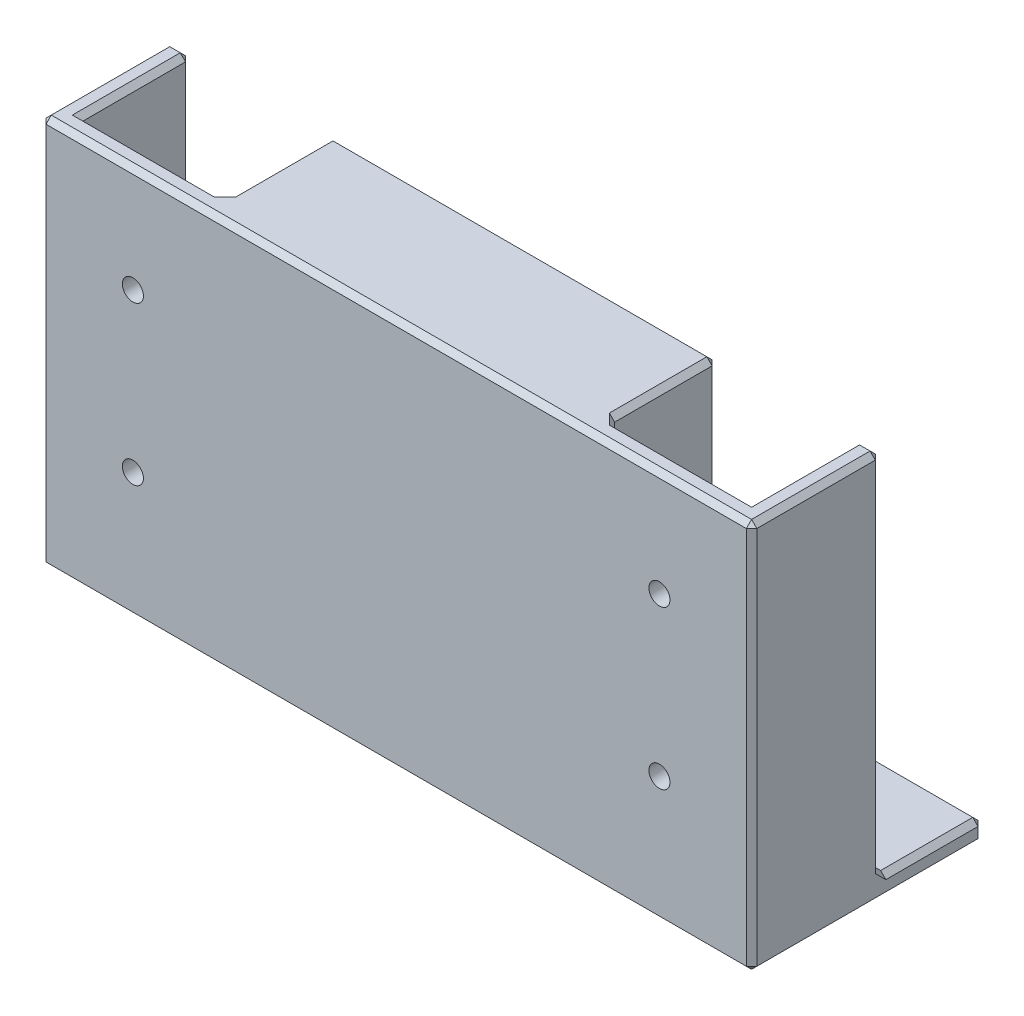
SolidWorks part; units mm, degrees
ref_plane "Front" through (0, 0, 0) normal (0, 0, 1) x (1, 0, 0)
ref_plane "Top" through (0, 0, 0) normal (0, 1, 0) x (1, 0, 0)
ref_plane "Right" through (0, 0, 0) normal (1, 0, 0) x (0, 0, -1)
sketch "Sketch1" plane through (0, 0, 0) normal (0, 1, 0) x (1, 0, 0)
  line L0 (-80.645, 15.56) -> (-85.725, 15.56)
  line L1 (85.725, 15.56) -> (80.645, 15.56)
  line L2 (85.725, 15.56) -> (85.725, -15.56)
  line L3 (85.725, -15.56) -> (-85.725, -15.56)
  line L4 (-85.725, 15.56) -> (-85.725, -15.56)
  line L5 (85.725, 15.56) -> (-85.725, -15.56) construction
  line L6 (85.725, -15.56) -> (-85.725, 15.56) construction
  line L7 (46.355, 15.56) -> (-46.355, 15.56)
  line L8 (-80.645, 15.56) -> (-80.645, -10.48)
  line L9 (-80.645, -10.48) -> (-46.355, -10.48)
  line L10 (-46.355, 15.56) -> (-46.355, -10.48)
  line L11 (-80.645, 15.56) -> (-46.355, -10.48) construction
  line L12 (-80.645, -10.48) -> (-46.355, 15.56) construction
  line L14 (80.645, 15.56) -> (80.645, -10.48)
  line L15 (80.645, -10.48) -> (46.355, -10.48)
  line L16 (46.355, 15.56) -> (46.355, -10.48)
  line L17 (80.645, 15.56) -> (46.355, -10.48) construction
  line L18 (80.645, -10.48) -> (46.355, 15.56) construction
  point P0 (0, 0)
  point P9 (-63.5, 2.54)
  point P14 (63.5, 2.54)
extrude "Boss-Extrude2" add sketch "Sketch1" along normal mid plane 88.9
shell "Shell3" thickness 5.08
sketch "Sketch7" plane through (0, -44.45, 0) normal (0, -1, 0) x (1, 0, 0)
  line L0 (80.645, 10.48) -> (46.355, 10.48) construction
  line L1 (85.725, 15.56) -> (-85.725, 15.56)
  line L2 (85.725, 15.56) -> (85.725, -40.32)
  line L3 (85.725, -40.32) -> (-85.725, -40.32)
  line L4 (-85.725, 15.56) -> (-85.725, -40.32)
  line L5 (85.725, 15.56) -> (-85.725, -40.32) construction
  line L6 (85.725, -40.32) -> (-85.725, 15.56) construction
  line L7 (-85.725, -15.56) -> (-85.725, 15.56) construction
  point P4 (0, -12.38)
  dimension "D1" = 50.8
extrude "Boss-Extrude3" add sketch "Sketch7" along normal blind 5.08
sketch "Sketch3" plane through (0, 0, 10.48) normal (0, 0, -1) x (-1, 0, 0)
  line L0 (-63.5, 44.45) -> (-63.5, -44.45) construction
  line L7 (-80.645, 44.45) -> (-46.355, 44.45) construction
  line L9 (-80.645, -44.45) -> (-46.355, -44.45) construction
  circle A0 centre (-63.5, 19.05) radius 2.54
  dimension "D1" = 5.08
  dimension "D2" = 25.4
extrude "Cut-Extrude2" cut sketch "Sketch3" against normal up to next (5.08 mm away)
mirror "Mirror3" about plane through (0, 0, 0) normal (0, 1, 0) of "Cut-Extrude2"
mirror "Mirror4" about plane through (0, 0, 0) normal (1, 0, 0) of "Mirror3", "Cut-Extrude2"
chamfer "Chamfer2" distance 1.27 angle 45 44 edges at (-85.725, -44.45, -27.94) (83.185, -44.45, -15.56) (63.5, -44.45, 10.48) (-63.5, -44.45, 10.48) (-80.645, -44.45, -2.54) (-46.355, 0, 10.48) (-46.355, -44.45, -2.54) (46.355, 0, 10.48) (46.355, -44.45, -2.54) (80.645, 0, -15.56) (80.645, -44.45, -2.54) (85.725, 0, -15.56) (85.725, -44.45, -27.94) (-85.725, -46.99, -40.32) (0, -49.53, -40.32) (0, -44.45, -40.32) (85.725, -46.99, -40.32) (85.725, -49.53, -12.38) (85.725, -2.54, 15.56) (-80.645, 0, -15.56) (-83.185, -44.45, -15.56) (-85.725, 0, -15.56) (-83.185, 44.45, -15.56) (-80.645, 44.45, -2.54) (-63.5, 44.45, 10.48) (-46.355, 44.45, -2.54) (-85.725, 44.45, 0) (0, 44.45, 15.56) (85.725, 44.45, 0) (83.185, 44.45, -15.56) (80.645, 44.45, -2.54) (63.5, 44.45, 10.48) (46.355, 44.45, -2.54) (46.355, 0, -15.56) (0, 44.45, -15.56) (-46.355, 0, -15.56) (0, -44.45, -15.56) (41.275, 0, 10.48) (0, 39.37, 10.48) (-41.275, 0, 10.48) (0, -39.37, 10.48) (0, -49.53, 15.56) (-85.725, -2.54, 15.56) (-85.725, -49.53, -12.38)
sketch "Sketch6" plane through (0, 0, 10.48) normal (0, 0, -1) x (-1, 0, 0)
  text T0 "3.65 In Spacing\r\n  5.0 In Center"
  point P1 (0, 0)
  point P2 (-31.321, 3.7673)
  point P3 (0, 0)
  point P4 (0, 0)
extrude "Cut-Extrude4" cut sketch "Sketch6" against normal blind 0.5
equation "\"D5@Sketch1\"=\"D2@Sketch1\""
equation "\"D3@Sketch1\"=\"D2@Sketch1\""
equation "\"D6@Sketch1\"=\"D2@Sketch1\""
equation "\"D8@Sketch1\"=\"D7@Sketch1\""
